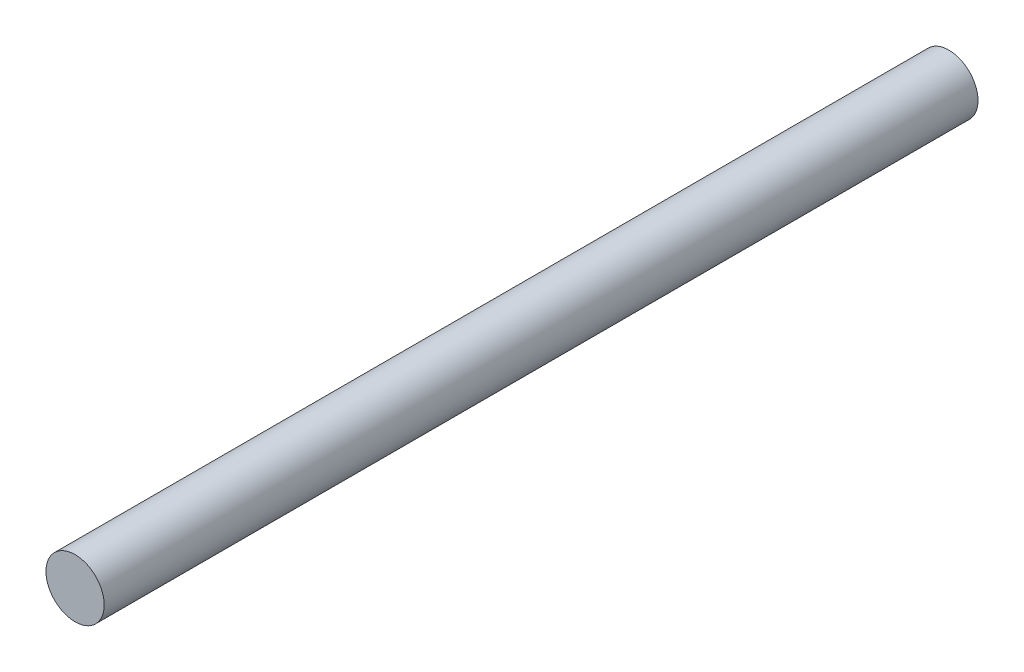
SolidWorks part; units mm, degrees
ref_plane "Front Plane" through (0, 0, 0) normal (0, 0, 1) x (1, 0, 0)
ref_plane "Top Plane" through (0, 0, 0) normal (0, 1, 0) x (1, 0, 0)
ref_plane "Right Plane" through (0, 0, 0) normal (1, 0, 0) x (0, 0, -1)
sketch "Sketch1" plane through (0, 0, 0) normal (0, 0, 1) x (1, 0, 0)
  circle A0 centre (0, 0) radius 4
  dimension "D1" = 8
extrude "Boss-Extrude1" add sketch "Sketch1" along normal blind 120
